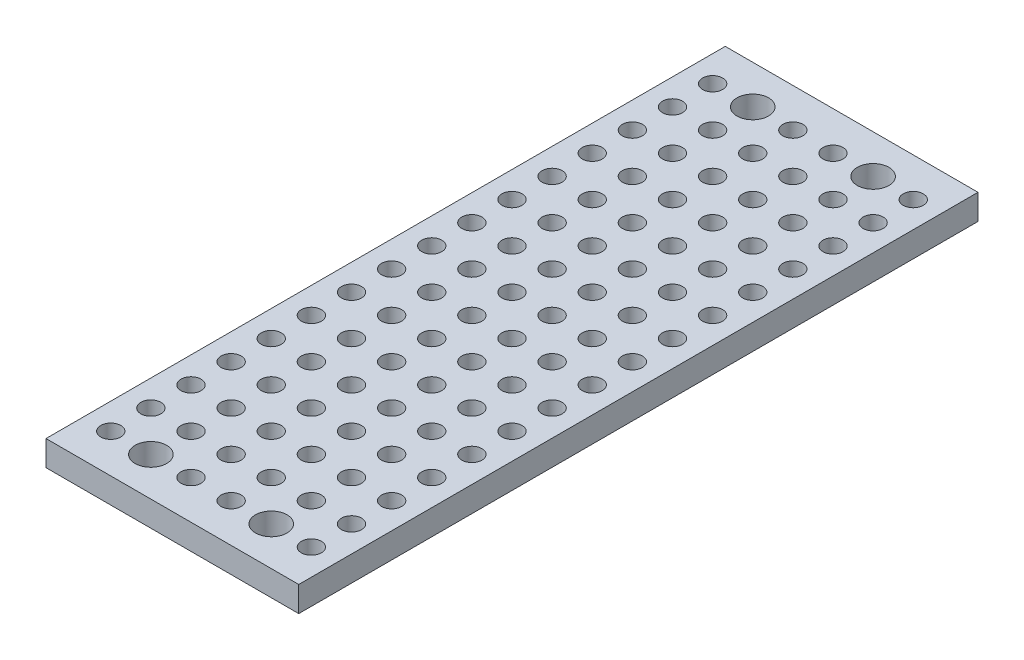
SolidWorks part; units mm, degrees
ref_plane "Front Plane" through (0, 0, 0) normal (0, 0, 1) x (1, 0, 0)
ref_plane "Top Plane" through (0, 0, 0) normal (0, 1, 0) x (1, 0, 0)
ref_plane "Right Plane" through (0, 0, 0) normal (1, 0, 0) x (0, 0, -1)
sketch "Sketch1" plane through (0, 0, 0) normal (0, 1, 0) x (1, 0, 0)
  line L1 (-8, -21.5) -> (8, -21.5)
  line L2 (-8, -21.5) -> (-8, 21.5)
  line L3 (-8, 21.5) -> (8, 21.5)
  line L4 (8, -21.5) -> (8, 21.5)
  line L5 (-8, -21.5) -> (8, 21.5) construction
  line L6 (-8, 21.5) -> (8, -21.5) construction
  point P0 (0, 0)
  dimension "D1" = 43
  dimension "D2" = 16
extrude "Boss-Extrude1" add sketch "Sketch1" along normal blind 1.6
hole_wizard "#6 (0.05) Diameter Hole1" positions "Sketch2" profile "Sketch3" hole size "#6" standard "ANSI Inch"
sketch "Sketch2" plane through (0, 1.6, 0) normal (0, 1, 0) x (1, 0, 0)
  line L2 (-6.35, 19.05) -> (-8, 21.5) construction
  line L4 (6.35, 19.05) -> (8, 21.5) construction
  line L6 (-6.35, -19.05) -> (-8, -21.5) construction
  line L8 (6.35, -19.05) -> (8, -21.5) construction
  point P0 (-6.35, 19.05)
  point P6 (-3.81, 19.05)
  point P7 (-1.27, 19.05)
  point P8 (1.27, 19.05)
  point P9 (3.81, 19.05)
  point P10 (6.35, 19.05)
  point P11 (-3.81, 16.51)
  point P12 (-1.27, 16.51)
  point P13 (1.27, 16.51)
  point P14 (3.81, 16.51)
  point P15 (6.35, 16.51)
  point P16 (-3.81, 13.97)
  point P17 (-1.27, 13.97)
  point P18 (1.27, 13.97)
  point P19 (3.81, 13.97)
  point P20 (6.35, 13.97)
  point P21 (-3.81, 11.43)
  point P22 (-1.27, 11.43)
  point P23 (1.27, 11.43)
  point P24 (3.81, 11.43)
  point P25 (6.35, 11.43)
  point P26 (-3.81, 8.89)
  point P27 (-1.27, 8.89)
  point P28 (1.27, 8.89)
  point P29 (3.81, 8.89)
  point P30 (6.35, 8.89)
  point P31 (-3.81, 6.35)
  point P32 (-1.27, 6.35)
  point P33 (1.27, 6.35)
  point P34 (3.81, 6.35)
  point P35 (6.35, 6.35)
  point P36 (-3.81, 3.81)
  point P37 (-1.27, 3.81)
  point P38 (1.27, 3.81)
  point P39 (3.81, 3.81)
  point P40 (6.35, 3.81)
  point P41 (-3.81, 1.27)
  point P42 (-1.27, 1.27)
  point P43 (1.27, 1.27)
  point P44 (3.81, 1.27)
  point P45 (6.35, 1.27)
  point P46 (-3.81, -1.27)
  point P47 (-1.27, -1.27)
  point P48 (1.27, -1.27)
  point P49 (3.81, -1.27)
  point P50 (6.35, -1.27)
  point P51 (-3.81, -3.81)
  point P52 (-1.27, -3.81)
  point P53 (1.27, -3.81)
  point P54 (3.81, -3.81)
  point P55 (6.35, -3.81)
  point P56 (-3.81, -6.35)
  point P57 (-1.27, -6.35)
  point P58 (1.27, -6.35)
  point P59 (3.81, -6.35)
  point P60 (6.35, -6.35)
  point P61 (-3.81, -8.89)
  point P62 (-1.27, -8.89)
  point P63 (1.27, -8.89)
  point P64 (3.81, -8.89)
  point P65 (6.35, -8.89)
  point P66 (-6.35, 16.51)
  point P67 (-6.35, 13.97)
  point P68 (-6.35, 11.43)
  point P69 (-6.35, 8.89)
  point P70 (-6.35, 6.35)
  point P71 (-6.35, 3.81)
  point P72 (-6.35, 1.27)
  point P73 (-6.35, -1.27)
  point P74 (-6.35, -3.81)
  point P75 (-6.35, -6.35)
  point P76 (-6.35, -8.89)
  point P96 (-6.35, -11.43)
  point P97 (-3.81, -11.43)
  point P98 (-1.27, -11.43)
  point P99 (1.27, -11.43)
  point P100 (3.81, -11.43)
  point P101 (6.35, -11.43)
  point P102 (-6.35, -13.97)
  point P103 (-3.81, -13.97)
  point P104 (-1.27, -13.97)
  point P105 (1.27, -13.97)
  point P106 (3.81, -13.97)
  point P107 (6.35, -13.97)
  point P108 (-6.35, -16.51)
  point P109 (-3.81, -16.51)
  point P110 (-1.27, -16.51)
  point P111 (1.27, -16.51)
  point P112 (3.81, -16.51)
  point P113 (6.35, -16.51)
  point P114 (-7.3144, -17.4945)
  point P115 (0, 0)
  point P116 (7.3215, -17.5216)
  point P117 (-6.35, -19.05)
  point P118 (-3.81, -19.05)
  point P119 (-1.27, -19.05)
  point P120 (1.27, -19.05)
  point P121 (3.81, -19.05)
  point P122 (6.35, -19.05)
  point P123 (-4.1844, -19.4569)
  point P124 (0, 0)
  point P125 (8.969, -19.0094)
  dimension "D3" = 2.54
  dimension "D4" = 2.54
  dimension "D1" = 6
  dimension "D2" = 16
sketch "Sketch3" plane through (-6.35, 1.6, -19.05) normal (1, 0, 0) x (0, 0, 1)
  line L0 (0, 0) -> (0, 26.7815)
  line L1 (0, 26.7815) -> (0.635, 26.4)
  line L2 (0.635, 26.4) -> (0.635, 0)
  line L5 (0.635, 0) -> (0, 0)
  line L10 (0, 26.7815) -> (-0.635, 26.4) construction
  line L11 (0, -6.35) -> (0, 107.95) construction
  dimension "Hole Dia." = 1.27
  dimension "Hole Depth" = 26.4
  dimension "Drill Angle" = 118
sketch "Sketch4" plane through (0, 1.6, 0) normal (0, 1, 0) x (1, 0, 0)
  circle A0 centre (-3.81, 19.05) radius 1
  circle A1 centre (3.81, 19.05) radius 1
  circle A2 centre (-3.81, -19.05) radius 1
  circle A3 centre (3.81, -19.05) radius 1
  dimension "D1" = 2
extrude "Cut-Extrude1" cut sketch "Sketch4" against normal through all
